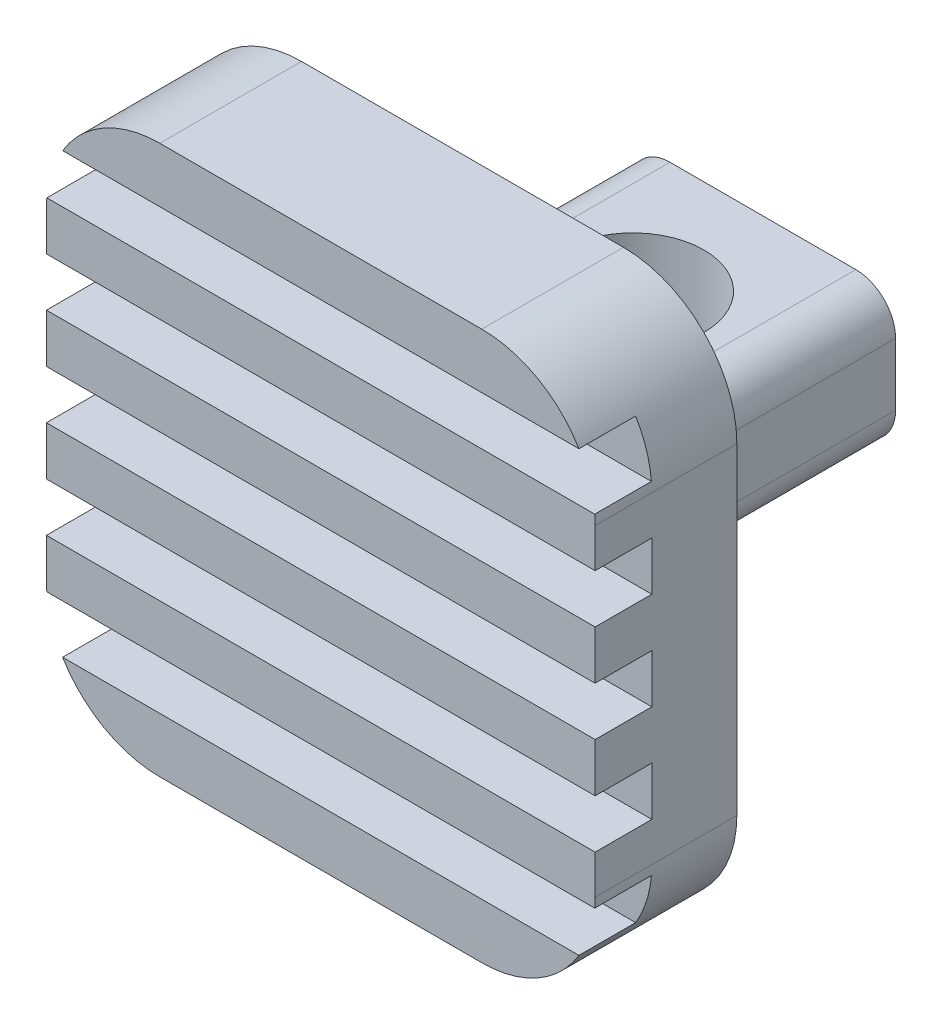
SolidWorks part; units mm, degrees
material "AISI 321 Annealed Stainless Steel (SS)"
ref_plane "Front Plane" through (0, 0, 0) normal (0, 0, 1) x (1, 0, 0)
ref_plane "Top Plane" through (0, 0, 0) normal (0, 1, 0) x (1, 0, 0)
ref_plane "Right Plane" through (0, 0, 0) normal (1, 0, 0) x (0, 0, -1)
sketch "Sketch1" plane through (0, 0, 0) normal (0, 1, 0) x (1, 0, 0)
  line L1 (-2.9718, -3.3655) -> (2.9718, -3.3655)
  line L2 (-2.9718, -3.3655) -> (-2.9718, 3.3655)
  line L3 (-2.9718, 3.3655) -> (2.9718, 3.3655)
  line L4 (2.9718, -3.3655) -> (2.9718, 3.3655)
  line L5 (-2.9718, -3.3655) -> (2.9718, 3.3655) construction
  line L6 (-2.9718, 3.3655) -> (2.9718, -3.3655) construction
  point P0 (0, 0)
  dimension "D1" = 5.9436
  dimension "D2" = 6.731
extrude "Boss-Extrude1" add sketch "Sketch1" along normal mid plane 3.175
sketch "Sketch2" plane through (0, 0, 3.3655) normal (0, 0, 1) x (1, 0, 0)
  line L1 (-6.1468, -6.1468) -> (6.1468, -6.1468)
  line L2 (-6.1468, -6.1468) -> (-6.1468, 6.1468)
  line L3 (-6.1468, 6.1468) -> (6.1468, 6.1468)
  line L4 (6.1468, -6.1468) -> (6.1468, 6.1468)
  line L5 (-6.1468, -6.1468) -> (6.1468, 6.1468) construction
  line L6 (-6.1468, 6.1468) -> (6.1468, -6.1468) construction
  point P0 (0, 0)
  dimension "D1" = 12.2936
extrude "Boss-Extrude2" add sketch "Sketch2" along normal blind 3.175
sketch "Sketch3" plane through (0, 1.5875, 0) normal (0, 1, 0) x (1, 0, 0)
  line L0 (2.9718, 3.3655) -> (-2.9718, 3.3655) construction
  circle A0 centre (0, 0.4445) radius 1.6002
  dimension "D2" = 3.2004
  dimension "D1" = 2.921
extrude "Cut-Extrude1" cut sketch "Sketch3" against normal through all both and the other way through all
fillet "Fillet1" radius 0.889 4 edges at (2.9718, -1.5875, 0) (-2.9718, -1.5875, 0) (-2.9718, 1.5875, 0) (2.9718, 1.5875, 0)
fillet "Fillet2" radius 0.635 8 edges at (0, 1.5875, 3.3655) (2.7114, 1.3271, 3.3655) (2.9718, 0, 3.3655) (2.7114, -1.3271, 3.3655) (0, -1.5875, 3.3655) (-2.7114, -1.3271, 3.3655) (-2.9718, 0, 3.3655) (-2.7114, 1.3271, 3.3655)
fillet "Fillet3" radius 2.54 4 edges at (6.1468, -6.1468, 4.953) (-6.1468, -6.1468, 4.953) (6.1468, 6.1468, 4.953) (-6.1468, 6.1468, 4.953)
sketch "Sketch4" plane through (0, 0, 0) normal (1, 0, 0) x (0, 0, -1)
  line L0 (-6.5405, -3.6068) -> (-6.5405, 3.6068) construction
  line L1 (-6.5405, -0.5461) -> (-5.2705, -0.5461)
  line L2 (-6.5405, -0.5461) -> (-6.5405, 0.5461)
  line L3 (-6.5405, 0.5461) -> (-5.2705, 0.5461)
  line L4 (-5.2705, -0.5461) -> (-5.2705, 0.5461)
  point P6 (-5.2705, 0)
  dimension "D1" = 1.0922
  dimension "D2" = 1.27
extrude "Cut-Extrude2" cut sketch "Sketch4" against normal through all both and the other way through all
pattern_linear "LPattern1" count 3 spacing 2.1844 along (0, -1, 0) count 3 spacing 2.1844 along (0, 1, 0) of "Cut-Extrude2"
equation "\"D3@LPattern1\" = \"D1@Sketch4\" * 2"
equation "\"D4@LPattern1\" = \"D1@Sketch4\" * 2"
